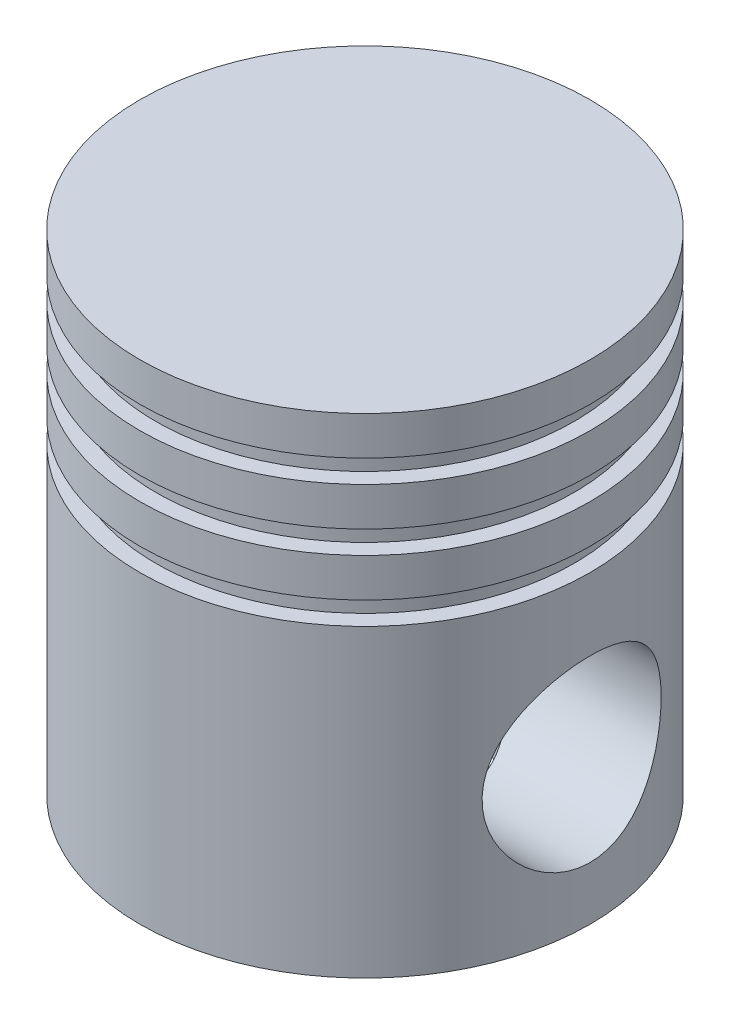
SolidWorks part; units mm, degrees
ref_plane "Front Plane" through (0, 0, 0) normal (0, 0, 1) x (1, 0, 0)
ref_plane "Top Plane" through (0, 0, 0) normal (0, 1, 0) x (1, 0, 0)
ref_plane "Right Plane" through (0, 0, 0) normal (1, 0, 0) x (0, 0, -1)
ref_axis "Axis1" through (0, -52.2211, 0) along (0, 1, 0)
sketch "Sketch2" plane through (0, 0, 0) normal (1, 0, 0) x (0, 0, -1)
  line L0 (39.5, 25.4289) -> (39.5, 21.1289)
  line L1 (0, 44.3289) -> (42.5, 44.3289)
  line L3 (0, -47.9711) -> (42.5, -47.9711)
  line L4 (42.5, 44.3289) -> (42.5, 37.0289)
  line L5 (39.5, 37.0289) -> (42.5, 37.0289)
  line L6 (39.5, 37.0289) -> (39.5, 32.7289)
  line L7 (39.5, 32.7289) -> (42.5, 32.7289)
  line L9 (39.5, 25.4289) -> (42.5, 25.4289)
  line L11 (39.5, 21.1289) -> (42.5, 21.1289)
  line L12 (39.5, 13.8289) -> (39.5, 9.5289)
  line L13 (39.5, 13.8289) -> (42.5, 13.8289)
  line L15 (39.5, 9.5289) -> (42.5, 9.5289)
  line L18 (42.5, 9.5289) -> (42.5, -47.9711)
  line L19 (42.5, 21.1289) -> (42.5, 13.8289)
  line L20 (42.5, 32.7289) -> (42.5, 25.4289)
  line L21 (0, 44.3289) -> (0, -47.9711)
  point P2 (41, 32.7289)
  dimension "D1" = 42.5
  dimension "D2" = 92.3
  dimension "D3" = 11.6
  dimension "D5" = 3
  dimension "D6" = 7.3
  dimension "D7" = 4.3
  dimension "D4" = 3
revolve "Revolve1" add sketch "Sketch2" angle 360 about axis through (0, -52.2211, 0) along (0, 1, 0)
sketch "Sketch4" plane through (0, 0, 0) normal (1, 0, 0) x (0, 0, -1)
  line L0 (-42.5, -47.9711) -> (42.5, -47.9711) construction
  line L1 (42.5, -47.9711) -> (42.5, 9.5289) construction
  circle A0 centre (0, -20.9711) radius 16.9
  dimension "D1" = 33.8
  dimension "D2" = 27
  dimension "D3" = 42.5
extrude "Cut-Extrude1" cut sketch "Sketch4" against normal mid plane 85
sketch "Sketch5" plane through (0, 0, 0) normal (1, 0, 0) x (0, 0, -1)
  line L0 (-42.5, 44.3289) -> (-42.5, 37.0289) construction
  line L1 (0, 37.0289) -> (-36, 37.0289)
  line L3 (0, -2.9711) -> (-36, -2.9711)
  line L4 (-36, 37.0289) -> (-36, -2.9711)
  line L5 (-42.5, -47.9711) -> (42.5, -47.9711) construction
  line L7 (0, 37.0289) -> (0, -2.9711)
  dimension "D2" = 6.5
  dimension "D3" = 85
  dimension "D4" = 45
  dimension "D5" = 36
revolve "Cut-Revolve1" cut sketch "Sketch5" angle 360 about axis through (0, -52.2211, 0) along (0, 1, 0)
sketch "Sketch6" plane through (0, -47.9711, 0) normal (0, -1, 0) x (1, 0, 0)
  circle A0 centre (0, 0) radius 25
  circle A1 centre (0, 0) radius 19
  dimension "D1" = 50
  dimension "D2" = 38
extrude "Cut-Extrude2" cut sketch "Sketch6" against normal blind 45 contours A1
